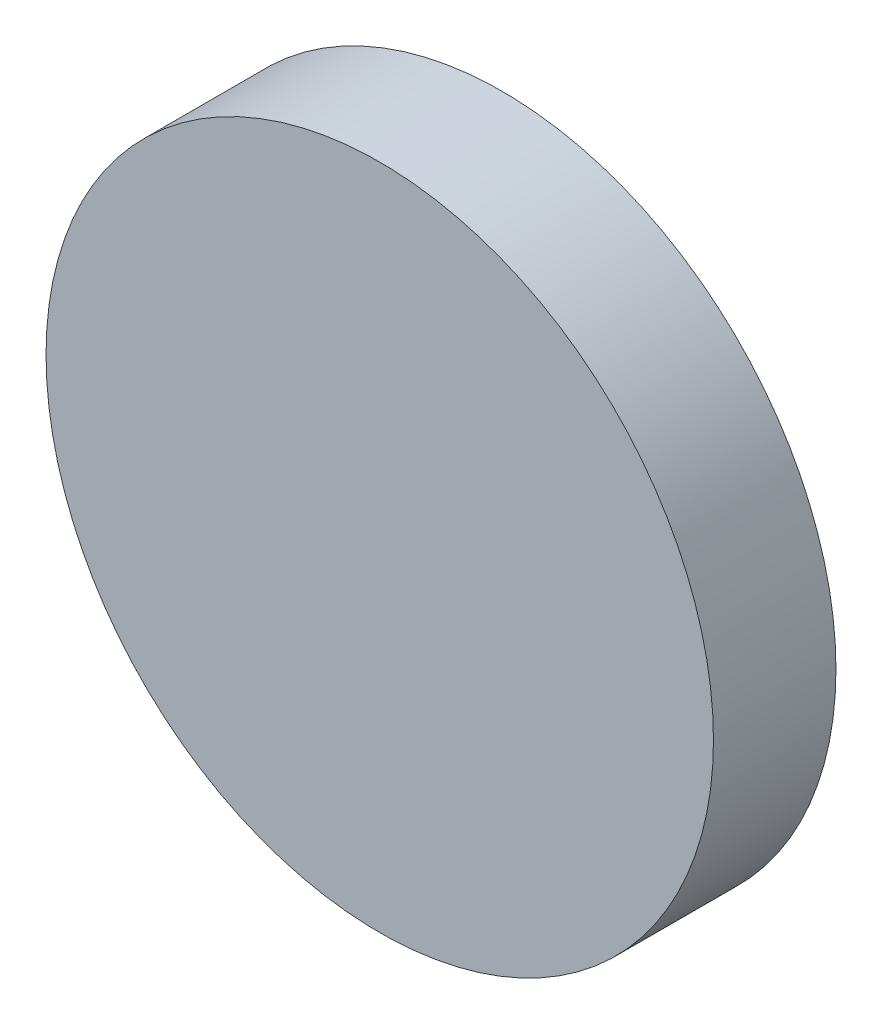
SolidWorks part; units mm, degrees
material "Bismuth"
ref_plane "Front" through (0, 0, 0) normal (0, 0, 1) x (1, 0, 0)
ref_plane "Top" through (0, 0, 0) normal (0, 1, 0) x (1, 0, 0)
ref_plane "Right" through (0, 0, 0) normal (1, 0, 0) x (0, 0, -1)
sketch "Sketch1" plane through (0, 0, 0) normal (0, 0, 1) x (1, 0, 0)
  circle A0 centre (0, 0) radius 133.5
extrude "Boss-Extrude1" add sketch "Sketch1" along normal blind 49
